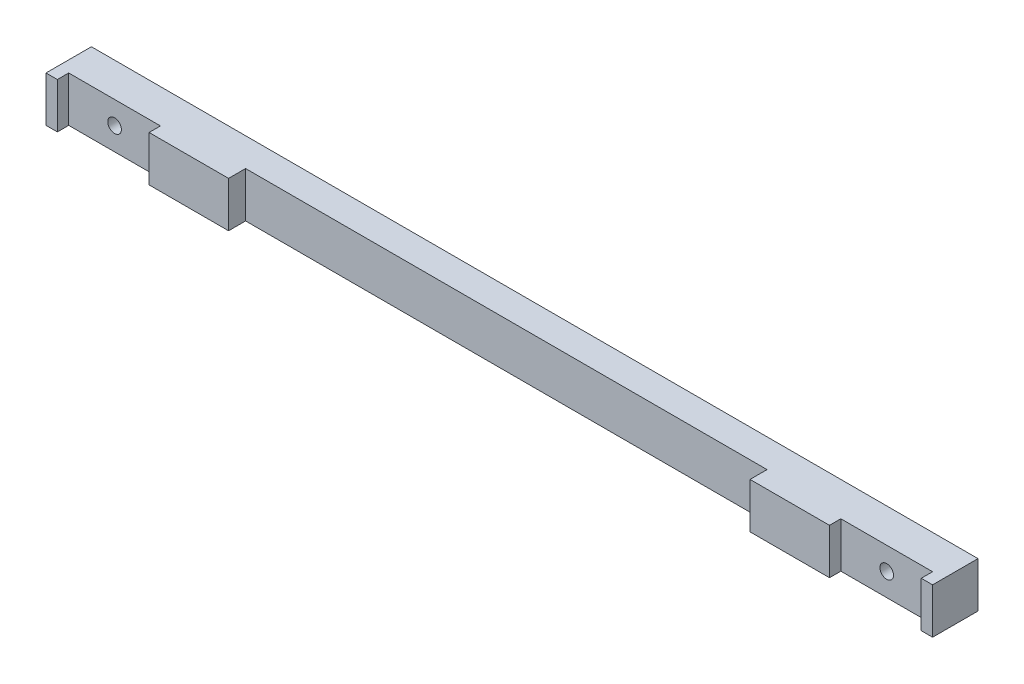
SolidWorks part; units mm, degrees
ref_plane "Front Plane" through (0, 0, 0) normal (0, 0, 1) x (1, 0, 0)
ref_plane "Top Plane" through (0, 0, 0) normal (0, 1, 0) x (1, 0, 0)
ref_plane "Right Plane" through (0, 0, 0) normal (1, 0, 0) x (0, 0, -1)
sketch "Sketch1" plane through (0, 0, 0) normal (0, 0, 1) x (1, 0, 0)
  line L1 (123.9647, -6.35) -> (-123.9647, -6.35)
  line L2 (123.9647, -6.35) -> (123.9647, 6.35)
  line L3 (123.9647, 6.35) -> (-123.9647, 6.35)
  line L4 (-123.9647, -6.35) -> (-123.9647, 6.35)
  line L5 (123.9647, -6.35) -> (-123.9647, 6.35) construction
  line L6 (123.9647, 6.35) -> (-123.9647, -6.35) construction
  point P0 (0, 0)
  dimension "D1" = 247.9294
  dimension "D2" = 12.7
extrude "Boss-Extrude1" add sketch "Sketch1" along normal blind 12.7
sketch "Sketch2" plane through (0, 0, 12.7) normal (0, 0, 1) x (1, 0, 0)
  line L0 (0, 19.2096) -> (0, -18.2275) construction
  line L1 (-95.1357, -10.7142) -> (-120.7897, -10.7142)
  line L2 (-95.1357, -10.7142) -> (-95.1357, 10.7142)
  line L3 (-95.1357, 10.7142) -> (-120.7897, 10.7142)
  line L4 (-120.7897, -10.7142) -> (-120.7897, 10.7142)
  line L5 (-95.1357, -10.7142) -> (-120.7897, 10.7142) construction
  line L6 (-95.1357, 10.7142) -> (-120.7897, -10.7142) construction
  line L7 (-123.9647, 6.35) -> (-123.9647, -6.35) construction
  line L8 (95.1357, 10.7142) -> (120.7897, -10.7142) construction
  line L9 (95.1357, -10.7142) -> (120.7897, 10.7142) construction
  line L10 (120.7897, -10.7142) -> (120.7897, 10.7142)
  line L11 (95.1357, 10.7142) -> (120.7897, 10.7142)
  line L12 (95.1357, -10.7142) -> (95.1357, 10.7142)
  line L13 (95.1357, -10.7142) -> (120.7897, -10.7142)
  point P0 (-107.9627, 0)
  point P14 (107.9627, 0)
  dimension "D1" = 3.175
  dimension "D2" = 25.654
extrude "Cut-Extrude1" cut sketch "Sketch2" against normal blind 3.175
sketch "Sketch3" plane through (0, 0, 12.7) normal (0, 0, 1) x (1, 0, 0)
  line L1 (72.9107, -11.2366) -> (-72.9107, -11.2366)
  line L2 (72.9107, -11.2366) -> (72.9107, 11.2366)
  line L3 (72.9107, 11.2366) -> (-72.9107, 11.2366)
  line L4 (-72.9107, -11.2366) -> (-72.9107, 11.2366)
  line L5 (72.9107, -11.2366) -> (-72.9107, 11.2366) construction
  line L6 (72.9107, 11.2366) -> (-72.9107, -11.2366) construction
  line L7 (95.1357, 6.35) -> (95.1357, -6.35) construction
  line L9 (-95.1357, -6.35) -> (-95.1357, 6.35) construction
  point P0 (0, 0)
  point P7 (95.1357, 0)
  dimension "D1" = 22.225
  dimension "D2" = 22.225
extrude "Cut-Extrude2" cut sketch "Sketch3" against normal blind 4.7625
sketch "Sketch4" plane through (0, 0, 9.525) normal (0, 0, 1) x (1, 0, 0)
  line L0 (-120.7897, 6.35) -> (-120.7897, -6.35) construction
  line L1 (0, 20.261) -> (0, -33.6484) construction
  circle A0 centre (-107.9627, 0) radius 1.905
  circle A1 centre (107.9627, 0) radius 1.905
  dimension "D2" = 3.81
  dimension "D1" = 12.827
extrude "Cut-Extrude3" cut sketch "Sketch4" against normal up to vertex
